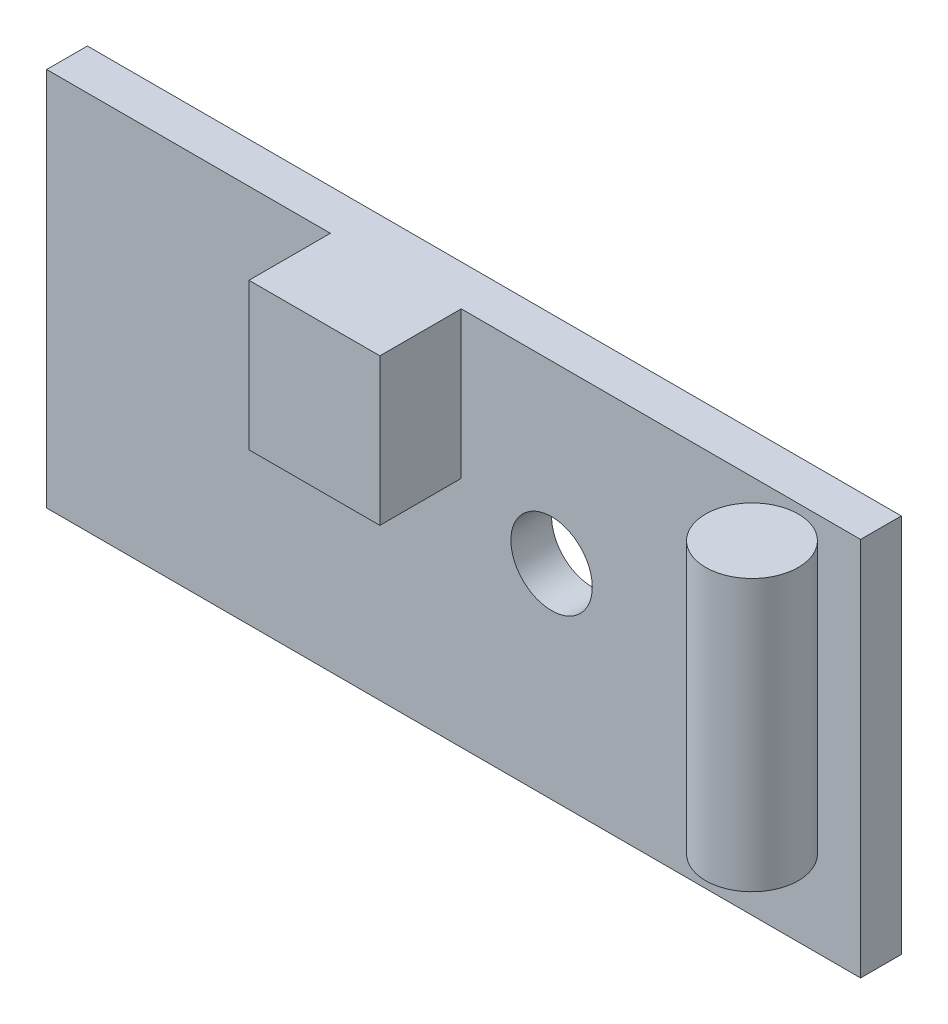
SolidWorks part; units mm, degrees
ref_plane "Front Plane" through (0, 0, 0) normal (0, 0, 1) x (1, 0, 0)
ref_plane "Top Plane" through (0, 0, 0) normal (0, 1, 0) x (1, 0, 0)
ref_plane "Right Plane" through (0, 0, 0) normal (1, 0, 0) x (0, 0, -1)
sketch "Sketch1" plane through (0, 0, 0) normal (0, 0, 1) x (1, 0, 0)
  line L1 (156.5188, 74.1843) -> (186.5188, 74.1843)
  line L2 (156.5188, 74.1843) -> (156.5188, 88.1843)
  line L3 (156.5188, 88.1843) -> (186.5188, 88.1843)
  line L4 (186.5188, 74.1843) -> (186.5188, 88.1843)
  circle A0 centre (175.1284, 81.7159) radius 1.5
extrude "Boss-Extrude1" add sketch "Sketch1" along normal blind 1.5
sketch "Sketch2" plane through (0, 0, 1.5) normal (0, 0, 1) x (1, 0, 0)
  line L0 (186.5188, 88.1843) -> (156.5188, 88.1843) construction
  line L1 (171.7989, 88.1843) -> (166.975, 88.1843)
  line L2 (171.7989, 88.1843) -> (171.7989, 82.7722)
  line L3 (171.7989, 82.7722) -> (166.975, 82.7722)
  line L4 (166.975, 88.1843) -> (166.975, 82.7722)
  dimension "D1" = 0
extrude "Boss-Extrude2" add sketch "Sketch2" along normal blind 3
sketch "Sketch3" plane through (0, 88.1843, 0) normal (0, 1, 0) x (1, 0, 0)
  circle A0 centre (184.5591, -3.5432) radius 1.7065
extrude "Boss-Extrude3" add sketch "Sketch3" against normal blind 10 separate body
